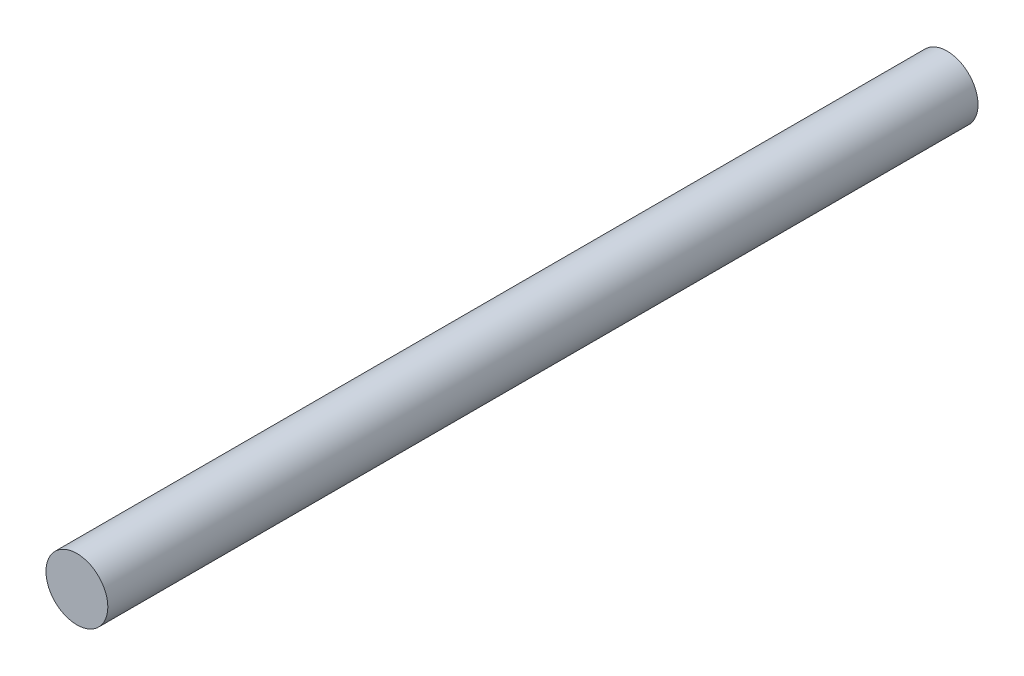
SolidWorks part; units mm, degrees
ref_plane "Front Plane" through (0, 0, 0) normal (0, 0, 1) x (1, 0, 0)
ref_plane "Top Plane" through (0, 0, 0) normal (0, 1, 0) x (1, 0, 0)
ref_plane "Right Plane" through (0, 0, 0) normal (1, 0, 0) x (0, 0, -1)
sketch "Sketch1" plane through (0, 0, 0) normal (0, 0, 1) x (1, 0, 0)
  circle A0 centre (0, 0) radius 1.6
extrude "Boss-Extrude1" add sketch "Sketch1" along normal blind 45
